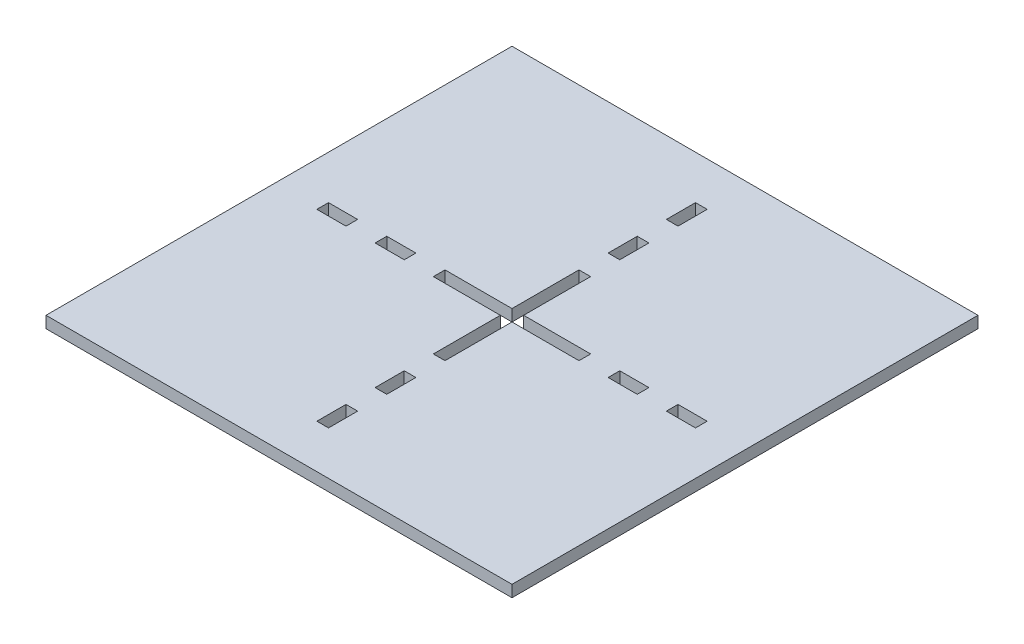
SolidWorks part; units mm, degrees
ref_plane "Front Plane" through (0, 0, 0) normal (0, 0, 1) x (1, 0, 0)
ref_plane "Top Plane" through (0, 0, 0) normal (0, 1, 0) x (1, 0, 0)
ref_plane "Right Plane" through (0, 0, 0) normal (1, 0, 0) x (0, 0, -1)
sketch "Sketch1" plane through (0, 0, 0) normal (0, 1, 0) x (1, 0, 0)
  line L0 (-80, 80) -> (80, -80) construction
  line L1 (-80, 80) -> (80, 80)
  line L2 (-80, 80) -> (-80, -80)
  line L3 (-80, -80) -> (80, -80)
  line L4 (80, 80) -> (80, -80)
  line L5 (-80, -80) -> (80, 80) construction
  point P4 (0, 0)
  dimension "D1" = 160
  dimension "D2" = 160
extrude "Boss-Extrude1" add sketch "Sketch1" along normal blind 4
sketch "Sketch3" plane through (0, 0, 0) normal (0, 0, 1) x (1, 0, 0)
  line L0 (0, 48.0064) -> (0, -50.269) construction
sketch "Sketch2" plane through (0, 4, 0) normal (0, 1, 0) x (1, 0, 0)
  line L0 (-2, 0) -> (2, -25) construction
  line L1 (-2, 0) -> (2, 0)
  line L2 (-2, 0) -> (-2, -25)
  line L3 (-2, -25) -> (2, -25)
  line L4 (2, 0) -> (2, -25)
  line L6 (-2, -45) -> (2, -45)
  line L7 (-2, -45) -> (-2, -35)
  line L8 (-2, -35) -> (2, -35)
  line L9 (2, -45) -> (2, -35)
  line L10 (-2, -65) -> (-2, -55)
  line L11 (-2, -55) -> (2, -55)
  line L12 (2, -65) -> (2, -55)
  line L13 (-2, -65) -> (2, -65)
  point P4 (0, 0)
  dimension "D1" = 4
  dimension "D2" = 25
  dimension "D3" = 10
  dimension "D4" = 35
  dimension "D5" = 2
extrude "Cut-Extrude1" cut sketch "Sketch2" against normal through all
pattern_circular "CirPattern1" count 4 over 360 about axis through (0, 0, 0) along (0, 1, 0) of "Cut-Extrude1"
